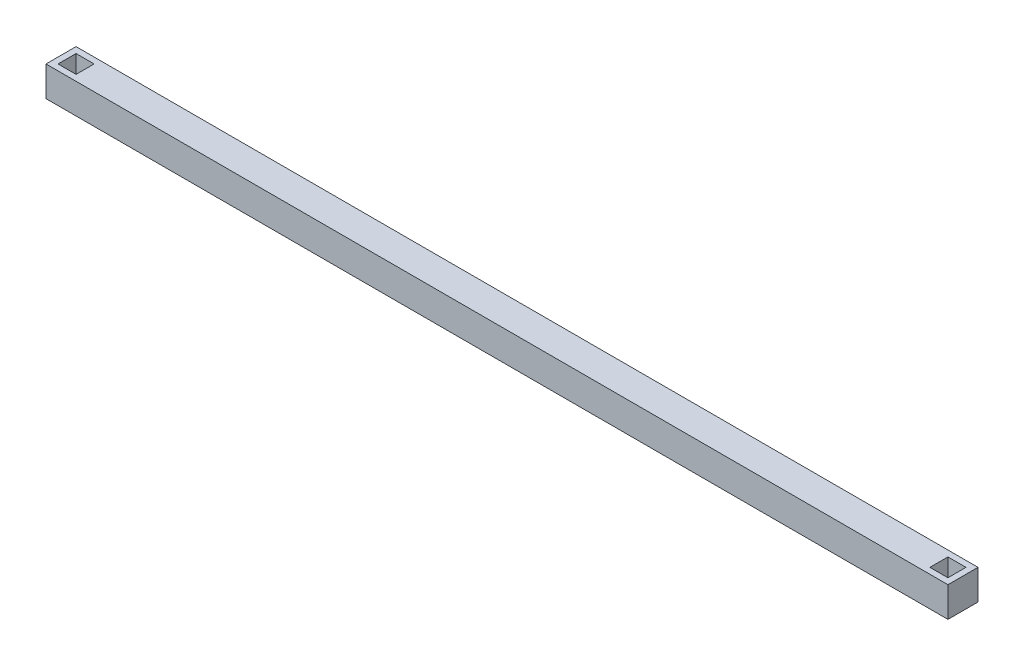
SolidWorks part; units mm, degrees
material "Дуб"
ref_plane "Спереди" through (0, 0, 0) normal (0, 0, 1) x (1, 0, 0)
ref_plane "Сверху" through (0, 0, 0) normal (0, 1, 0) x (1, 0, 0)
ref_plane "Справа" through (0, 0, 0) normal (1, 0, 0) x (0, 0, -1)
sketch "Эскиз1" plane through (0, 0, 0) normal (0, 0, 1) x (1, 0, 0)
  line L0 (0, 165.6487) -> (0, -163.9792) construction
  line L1 (-750, 25) -> (750, 25)
  line L2 (-750, 25) -> (-750, -25)
  line L3 (-750, -25) -> (750, -25)
  line L4 (750, 25) -> (750, -25)
  line L5 (-750, 25) -> (750, -25) construction
  line L6 (-750, -25) -> (750, 25) construction
  point P0 (0, 0)
  dimension "D1" = 1500
  dimension "D2" = 50
extrude "Бобышка-Вытянуть6" add sketch "Эскиз1" along normal blind 50
sketch "Эскиз6" plane through (0, 25, 0) normal (0, 1, 0) x (1, 0, 0)
  line L0 (750, 0) -> (-750, 0) construction
  line L1 (750, -50) -> (-750, -50) construction
  line L2 (710, -10) -> (740, -10)
  line L3 (710, -10) -> (710, -40)
  line L4 (710, -40) -> (740, -40)
  line L5 (750, -50) -> (750, 0) construction
  line L6 (-750, -50) -> (-750, 0) construction
  line L7 (-740, -10) -> (-710, -10)
  line L8 (-740, -10) -> (-740, -40)
  line L9 (-740, -40) -> (-710, -40)
  line L10 (-710, -10) -> (-710, -40)
  line L11 (740, -10) -> (740, -40)
  line L12 (710, -10) -> (740, -40) construction
  line L13 (710, -40) -> (740, -10) construction
  point P0 (725, -25)
  dimension "D1" = 30
  dimension "D2" = 30
  dimension "D3" = 10
  dimension "D4" = 10
  dimension "D5" = 30
  dimension "D6" = 30
  dimension "D7" = 10
  dimension "D8" = 10
extrude "Вырез-Вытянуть2" cut sketch "Эскиз6" against normal blind 30 contours L8 L9 L10 L7 | L3 L4 L11 L2
